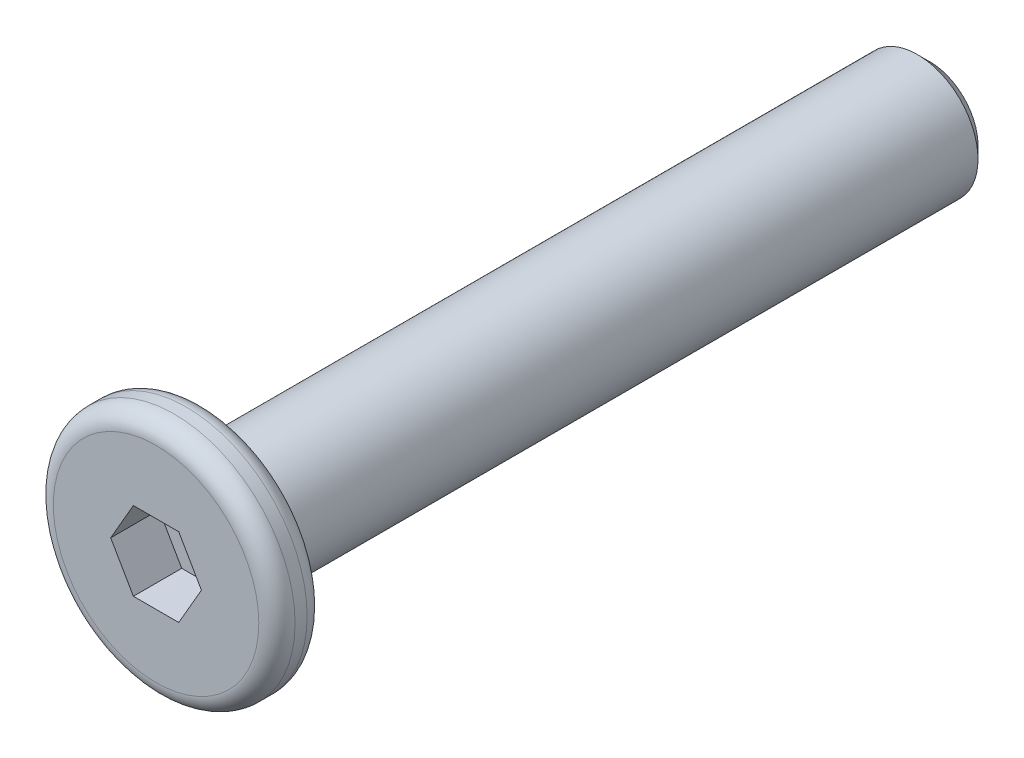
SolidWorks part; units mm, degrees
ref_plane "前视基准面" through (0, 0, 0) normal (0, 0, 1) x (1, 0, 0)
ref_plane "上视基准面" through (0, 0, 0) normal (0, 1, 0) x (1, 0, 0)
ref_plane "右视基准面" through (0, 0, 0) normal (1, 0, 0) x (0, 0, -1)
sketch "草图1" plane through (0, 0, 0) normal (0, 0, 1) x (1, 0, 0)
  circle A0 centre (0, 0) radius 2
  dimension "D1" = 4
extrude "凸台-拉伸1" add sketch "草图1" along normal mid plane 0.8
sketch "草图2" plane through (0, 0, -0.4) normal (0, 0, -1) x (-1, 0, 0)
  circle A0 centre (0, 0) radius 1
  dimension "D1" = 2
extrude "凸台-拉伸2" add sketch "草图2" along normal blind 12
chamfer "倒角1" distance 0.2 angle 45 1 edges at (-1, 0, -12.4)
sketch "草图3" plane through (0, 0, 0.4) normal (0, 0, 1) x (1, 0, 0)
  line L1 (0.7506, 0) -> (0.3753, 0.65)
  line L2 (0.3753, 0.65) -> (-0.3753, 0.65)
  line L3 (-0.3753, 0.65) -> (-0.7506, 0)
  line L4 (-0.7506, 0) -> (-0.3753, -0.65)
  line L5 (-0.3753, -0.65) -> (0.3753, -0.65)
  line L6 (0.3753, -0.65) -> (0.7506, 0)
  circle A0 centre (0, 0) radius 0.65 construction
  dimension "D1" = 1.3
extrude "切除-拉伸1" cut sketch "草图3" against normal blind 0.8
fillet "圆角2" radius 0.3 2 edges at (2, 0, -0.4) (2, 0, 0.4)
